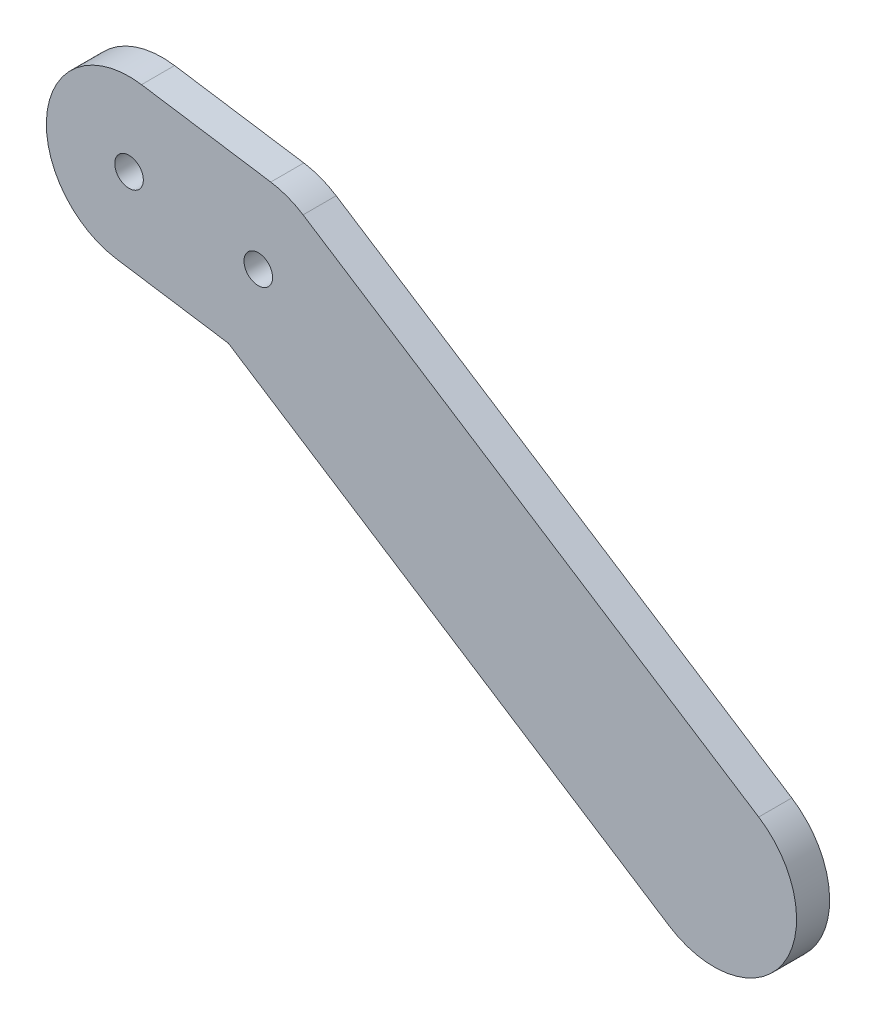
SolidWorks part; units mm, degrees
ref_plane "Front Plane" through (0, 0, 0) normal (0, 0, 1) x (1, 0, 0)
ref_plane "Top Plane" through (0, 0, 0) normal (0, 1, 0) x (1, 0, 0)
ref_plane "Right Plane" through (0, 0, 0) normal (1, 0, 0) x (0, 0, -1)
sketch "Sketch1" plane through (0, 0, 0) normal (0, 0, 1) x (1, 0, 0)
  line L0 (0, 0) -> (-15.6333, 2.3847) construction
  line L3 (-1.5079, -9.8857) -> (-17.1412, -7.501)
  line L6 (1.5079, 9.8857) -> (-14.1254, 12.2703)
  line L7 (0, 0) -> (55.1043, -35.5221) construction
  line L8 (5.4181, 8.405) -> (60.5224, -27.1171)
  line L9 (-5.4181, -8.405) -> (49.6862, -43.9271)
  arc A6 (-1.5079, -9.8857) -> (1.5079, 9.8857) centre (0, 0) ccw
  arc A7 (-14.1254, 12.2703) -> (-17.1412, -7.501) centre (-15.6333, 2.3847) ccw
  arc A8 (5.4181, 8.405) -> (-5.4181, -8.405) centre (0, 0) ccw
  arc A9 (49.6862, -43.9271) -> (60.5224, -27.1171) centre (55.1043, -35.5221) ccw
  circle A10 centre (0, 0) radius 1.73
  circle A11 centre (-15.6333, 2.3847) radius 1.73
  point P2 (-7.8167, 1.1923)
  point P8 (27.5522, -17.761)
  dimension "D1" = 3.46
  dimension "D2" = 3.46
  dimension "D3" = 20
  dimension "D4" = 20
extrude "Boss-Extrude1" add sketch "Sketch1" along normal mid plane 4 contours A8 L6 A7 L3 L9 A11 | A6 A8 L9 L3 A10 | L9 A9 L8 A6 L3
